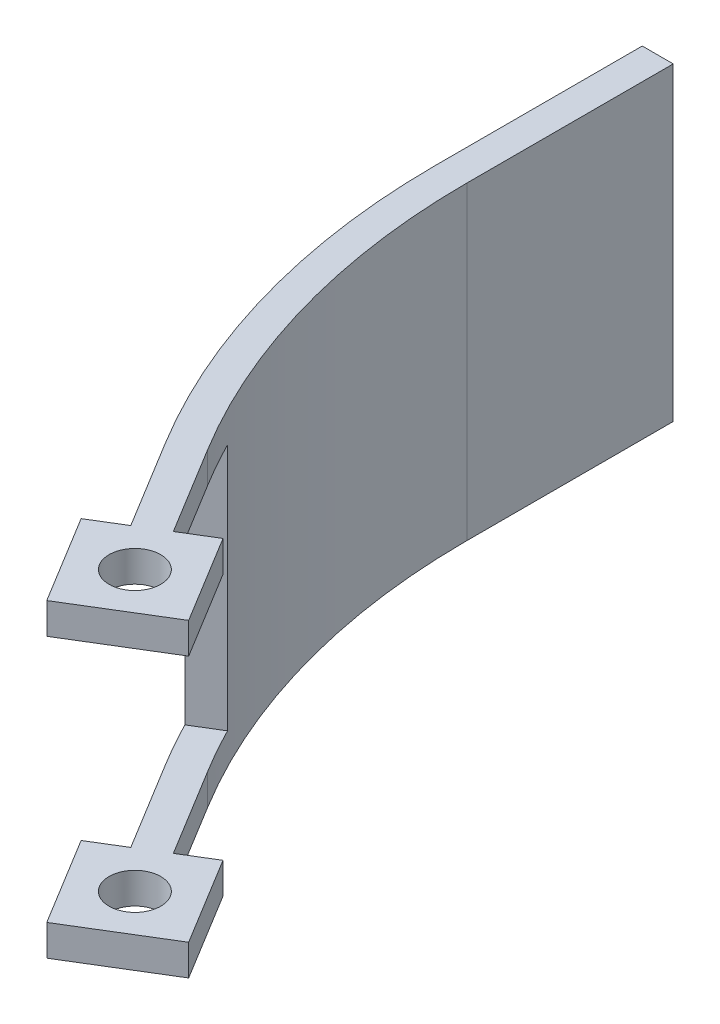
SolidWorks part; units mm, degrees
ref_plane "Face" through (0, 0, 0) normal (0, 0, 1) x (1, 0, 0)
ref_plane "Dessus" through (0, 0, 0) normal (0, 1, 0) x (1, 0, 0)
ref_plane "Droite" through (0, 0, 0) normal (1, 0, 0) x (0, 0, -1)
sketch "Esquisse1" plane through (0, 0, 0) normal (0, 1, 0) x (1, 0, 0)
  line L0 (0, 0) -> (0, 20)
  line L1 (0, 20) -> (3, 20)
  line L2 (3, 20) -> (3, 0)
  line L3 (10.2473, -36.4639) -> (12.8081, -34.9012) construction
  line L4 (18.0173, -43.4373) -> (21.0049, -41.6141)
  line L5 (10.2473, -36.4639) -> (15.4564, -45)
  line L6 (12.8081, -34.9012) -> (18.0173, -43.4373)
  line L7 (21.0049, -41.6141) -> (26.214, -50.1502)
  line L8 (26.214, -50.1502) -> (17.6779, -55.3593)
  line L9 (17.6779, -55.3593) -> (12.4688, -46.8232)
  line L10 (12.4688, -46.8232) -> (15.4564, -45)
  line L11 (15.0734, -51.0912) -> (23.6095, -45.8821) construction
  arc A0 (0, 0) -> (10.2473, -36.4639) centre (70, 0) ccw
  arc A1 (3, 0) -> (12.8081, -34.9012) centre (70, 0) ccw
  circle A2 centre (19.3414, -48.4867) radius 2.5
  dimension "D2" = 70
  dimension "D8" = 5
  dimension "D1" = 20
  dimension "D3" = 10
  dimension "D4" = 3
  dimension "D5" = 3
  dimension "D6" = 65
  dimension "D7" = 10
extrude "Extrusion1" add sketch "Esquisse1" along normal blind 30
sketch "Esquisse3" plane through (-11.7348, 0, 7.1612) normal (-0.8536, 0, 0.5209) x (0.5209, 0, 0.8536)
  line L0 (56.4639, 30) -> (56.4639, 0) construction
  line L1 (56.4639, 27) -> (31.4639, 27)
  line L2 (56.4639, 27) -> (56.4639, 3)
  line L3 (56.4639, 3) -> (31.4639, 3)
  line L4 (31.4639, 27) -> (31.4639, 3)
  line L5 (46.4639, 30) -> (56.4639, 30) construction
  line L6 (46.4639, 0) -> (56.4639, 0) construction
  dimension "D1" = 3
  dimension "D2" = 3
  dimension "D3" = 25
extrude "Extrusion2" cut sketch "Esquisse3" against normal through all
